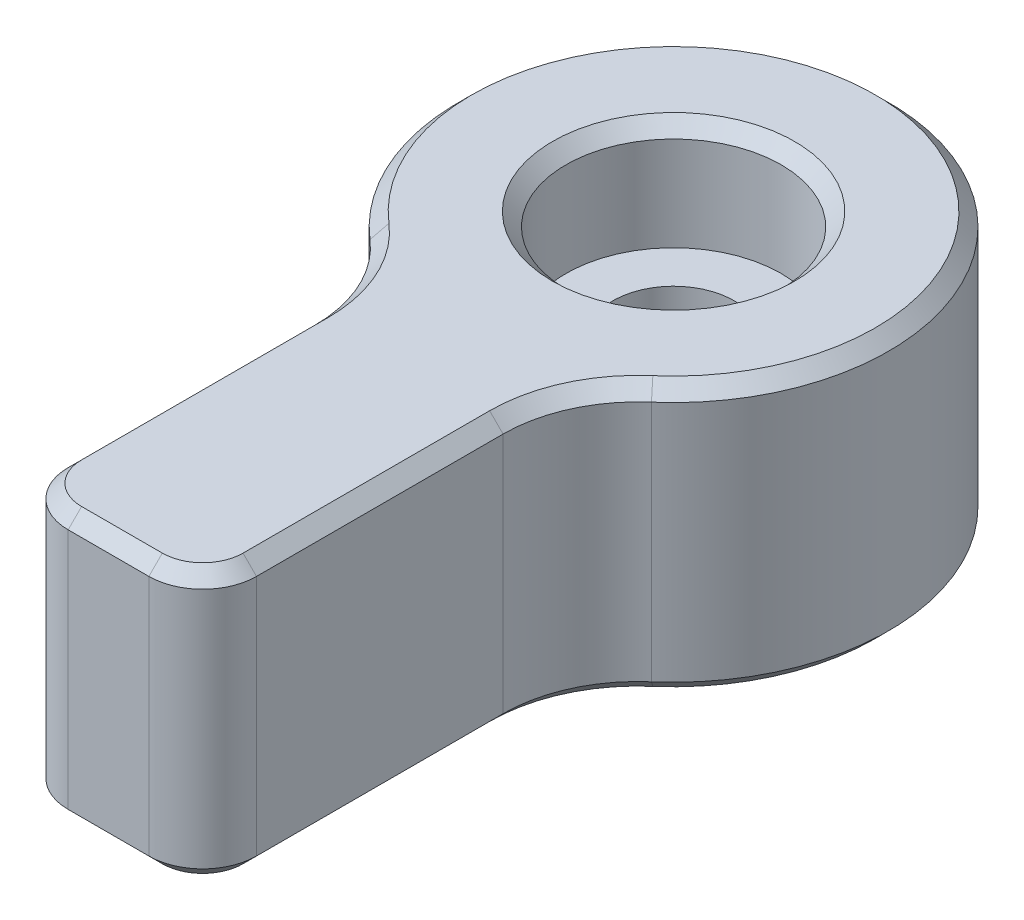
SolidWorks part; units mm, degrees
material "Сплав 2024"
ref_plane "Спереди" through (0, 0, 0) normal (0, 0, 1) x (1, 0, 0)
ref_plane "Сверху" through (0, 0, 0) normal (0, 1, 0) x (1, 0, 0)
ref_plane "Справа" through (0, 0, 0) normal (1, 0, 0) x (0, 0, -1)
sketch "Эскиз1" plane through (0, 0, 0) normal (0, 1, 0) x (1, 0, 0)
  line L0 (0, 18.3103) -> (0, -37.454) construction
  line L3 (-3.5, -7.1937) -> (-3.5, -21)
  line L4 (-3.5, -21) -> (3.5, -21)
  line L5 (3.5, -7.1937) -> (3.5, -21)
  arc A0 (3.5, -7.1937) -> (-3.5, -7.1937) centre (0, 0) ccw
  point P1 (0, -21)
  dimension "D1" = 16
  dimension "D2" = 7
  dimension "D3" = 21
extrude "Бобышка-Вытянуть1" add sketch "Эскиз1" along normal blind 10
hole_wizard "Цековка для винта с внутренним шестигранником M41" positions "Эскиз3" profile "Эскиз2" counterbore size "M4" standard "Ansi Metric" end condition through all
sketch "Эскиз3" plane through (0, 10, 0) normal (0, 1, 0) x (1, 0, 0)
  point P0 (0, 0)
sketch "Эскиз2" plane through (0, 10, 0) normal (1, 0, 0) x (0, 0, 1)
  line L0 (0, 0) -> (0, 10)
  line L1 (0, 10) -> (2.25, 10)
  line L3 (2.25, 10) -> (2.25, 4)
  line L4 (2.25, 4) -> (4, 4)
  line L5 (4, 4) -> (4, 0)
  line L7 (4, 0) -> (0, 0)
  line L11 (0, -6.35) -> (0, 107.95) construction
  dimension "Диаметр сквозного отверстия" = 4.5
  dimension "Глубина сквозного отверстия" = 10
  dimension "Диаметр цековки" = 8
  dimension "Глубина цековки" = 4
fillet "Скругление1" radius 2 2 edges at (3.5, 5, 21) (-3.5, 5, 21)
fillet "Скругление2" radius 5 2 edges at (3.5, 5, 7.1937) (-3.5, 5, 7.1937)
chamfer "Фаска1" distance 0.5 angle 45 18 edges at (3.9532, 0, 7.756) (0, 0, -8) (-3.9532, 0, 7.756) (-3.5, 0, 14.4181) (-2.9142, 0, 20.4142) (0, 0, 21) (2.9142, 0, 20.4142) (3.5, 0, 14.4181) (0, 0, 2.25) (-2.9142, 10, 20.4142) (-3.5, 10, 14.4181) (-3.9532, 10, 7.756) (0, 10, -8) (3.9532, 10, 7.756) (3.5, 10, 14.4181) (2.9142, 10, 20.4142) (0, 10, 21) (0, 10, 4)
